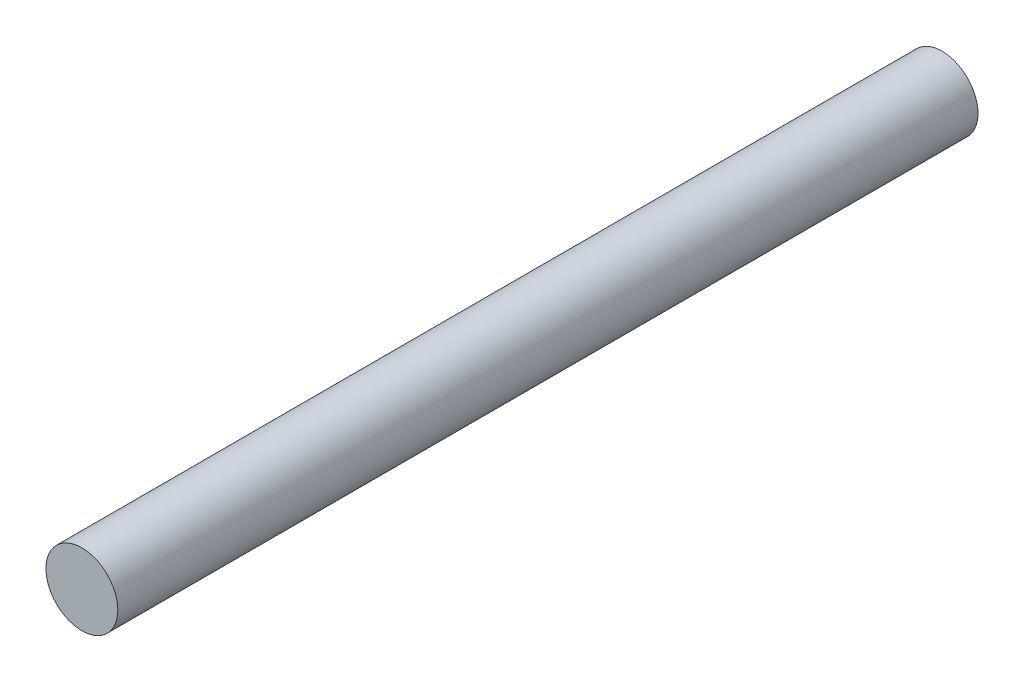
SolidWorks part; units mm, degrees
material "Polyurethane Foam Flexible"
ref_plane "Front Plane" through (0, 0, 0) normal (0, 0, 1) x (1, 0, 0)
ref_plane "Top Plane" through (0, 0, 0) normal (0, 1, 0) x (1, 0, 0)
ref_plane "Right Plane" through (0, 0, 0) normal (1, 0, 0) x (0, 0, -1)
sketch "Sketch1" plane through (0, 0, 0) normal (0, 0, 1) x (1, 0, 0)
  circle A0 centre (0, 0) radius 31.75
  dimension "D1" = 63.5
extrude "Boss-Extrude1" add sketch "Sketch1" along normal blind 760
